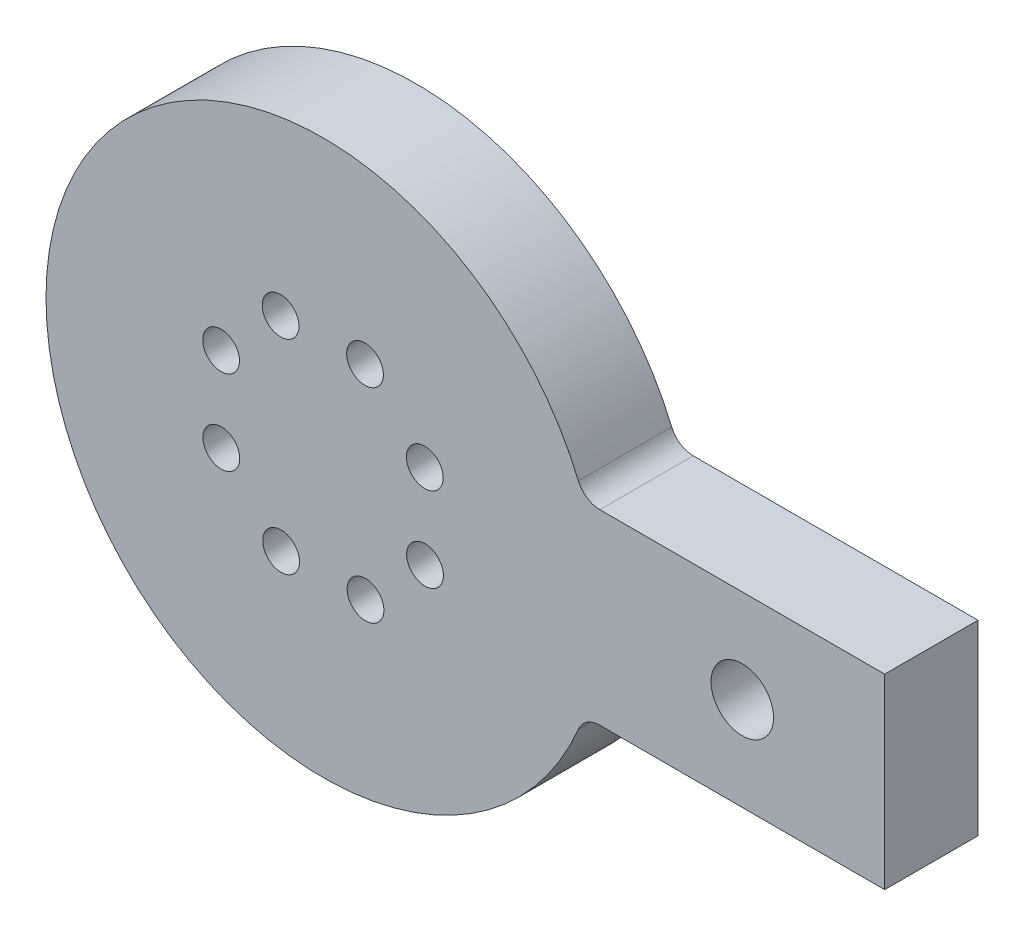
SolidWorks part; units mm, degrees
ref_plane "Front Plane" through (0, 0, 0) normal (0, 0, 1) x (1, 0, 0)
ref_plane "Top Plane" through (0, 0, 0) normal (0, 1, 0) x (1, 0, 0)
ref_plane "Right Plane" through (0, 0, 0) normal (1, 0, 0) x (0, 0, -1)
sketch "Sketch1" plane through (0, 0, 0) normal (0, 0, 1) x (1, 0, 0)
  line L0 (0, 0) -> (56.2713, 0) construction
  line L2 (-1.0173, -12.7) -> (76.4173, -12.7)
  line L3 (-1.0173, -12.7) -> (-1.0173, 12.7)
  line L4 (-1.0173, 12.7) -> (76.4173, 12.7)
  line L5 (76.4173, -12.7) -> (76.4173, 12.7)
  line L6 (-1.0173, -12.7) -> (76.4173, 12.7) construction
  line L7 (-1.0173, 12.7) -> (76.4173, -12.7) construction
  circle A0 centre (0, 0) radius 37.7
  circle A2 centre (-5.7751, 13.8437) radius 2.5
  circle A3 centre (5.7053, 13.8726) radius 2.5
  circle A4 centre (13.8437, 5.7751) radius 2.5
  circle A5 centre (13.8726, -5.7053) radius 2.5
  circle A6 centre (5.7751, -13.8437) radius 2.5
  circle A7 centre (-5.7053, -13.8726) radius 2.5
  circle A9 centre (-13.8437, -5.7751) radius 2.5
  circle A10 centre (-13.8726, 5.7053) radius 2.5
  circle A11 centre (0, 0) radius 25
  point P28 (37.7, 0)
  dimension "D1" = 12.7
extrude "Boss-Extrude1" add sketch "Sketch1" along normal blind 12.7 contours A11 L4 A0 L2 | A0 L2 L5 L4 | A11 L2 A0 L4 | L2 A11 L4 A3 L3 A6 A4 A5 | L4 A11 L2 A6 L3 A3 A2 A7 A9 A10
fillet "Fillet1" radius 3.175 2 edges at (35.4965, -12.7, 6.35) (35.4965, 12.7, 6.35)
sketch "Sketch2" plane through (0, 0, 12.7) normal (0, 0, 1) x (1, 0, 0)
  line L0 (57.0418, 12.7) -> (57.0418, -12.7) construction
  line L1 (37.6663, 12.7) -> (76.4173, 12.7) construction
  line L2 (37.6663, -12.7) -> (76.4173, -12.7) construction
  point P0 (57.0418, 0)
  dimension "D1" = 0
hole_wizard "Tap Drill for M10x1.5 Tap1" positions "Sketch4" profile "Sketch3" hole size "M10x1.5" standard "ANSI Metric"
sketch "Sketch4" plane through (0, 0, 12.7) normal (0, 0, 1) x (1, 0, 0)
  line L0 (57.0418, 12.7) -> (57.0418, -12.7) construction
  point P0 (57.0418, 0)
sketch "Sketch3" plane through (57.0418, 0, 12.7) normal (1, 0, 0) x (0, -1, 0)
  line L0 (0, 0) -> (0, 22.5537)
  line L1 (0, 22.5537) -> (4.25, 20)
  line L2 (4.25, 20) -> (4.25, 0)
  line L5 (4.25, 0) -> (0, 0)
  line L10 (0, 22.5537) -> (-4.25, 20) construction
  line L11 (0, -6.35) -> (0, 107.95) construction
  dimension "Hole Dia." = 8.5
  dimension "Hole Depth" = 20
  dimension "Drill Angle" = 118
